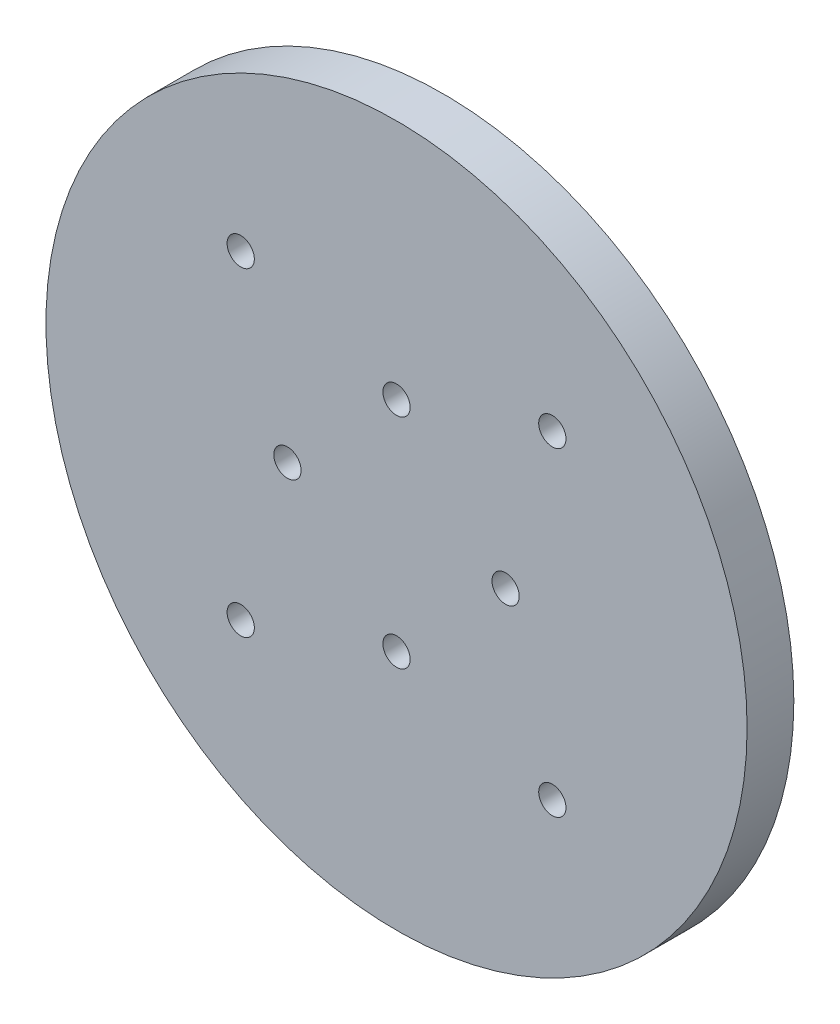
SolidWorks part; units mm, degrees
ref_plane "Front Plane" through (0, 0, 0) normal (0, 0, 1) x (1, 0, 0)
ref_plane "Top Plane" through (0, 0, 0) normal (0, 1, 0) x (1, 0, 0)
ref_plane "Right Plane" through (0, 0, 0) normal (1, 0, 0) x (0, 0, -1)
sketch "Sketch1" plane through (0, 0, 0) normal (0, 0, 1) x (1, 0, 0)
  circle A0 centre (0, 0) radius 45
  dimension "D1" = 90
extrude "Boss-Extrude1" add sketch "Sketch1" along normal blind 6
sketch "Sketch2" plane through (0, 0, 0) normal (0, 0, -1) x (-1, 0, 0)
  circle A0 centre (0, 0) radius 22
  dimension "D1" = 44
extrude "Boss-Extrude2" add sketch "Sketch2" along normal blind 6
sketch "Sketch3" plane through (0, 0, -6) normal (0, 0, -1) x (-1, 0, 0)
  circle A0 centre (0, 0) radius 20.1
  dimension "D1" = 40.2
extrude "Boss-Extrude3" add sketch "Sketch3" along normal blind 4.7
sketch "Sketch4" plane through (0, 0, -10.7) normal (0, 0, -1) x (-1, 0, 0)
  circle A0 centre (0, 0) radius 18.1
  dimension "D1" = 36.2
extrude "Cut-Extrude1" cut sketch "Sketch4" against normal blind 11
sketch "Sketch5" plane through (0, 0, 0.3) normal (0, 0, -1) x (-1, 0, 0)
  circle A4 centre (14, 0) radius 1.75
  circle A5 centre (0, -14) radius 1.75
  circle A6 centre (-14, 0) radius 1.75
  circle A7 centre (0, 14) radius 1.75
  point P11 (0, 0)
  point P12 (0, 0)
  dimension "D1" = 3.5
  dimension "D2" = 14
  dimension "D3" = 4
extrude "Cut-Extrude2" cut sketch "Sketch5" against normal through all
sketch "Sketch6" plane through (0, 0, 0.3) normal (0, 0, -1) x (-1, 0, 0)
  line L0 (20, -20.5) -> (20, 20.5)
  line L1 (0, 0) -> (0, -39.3338)
  circle A0 centre (20, -20.5) radius 1.75
  circle A1 centre (-20, 20.5) radius 1.75
  circle A2 centre (-20, -20.5) radius 1.75
  circle A3 centre (20, 20.5) radius 1.75
  point P3 (20, 0)
  dimension "D3" = 3.5
  dimension "D1" = 41
  dimension "D2" = 20
  dimension "D5" = 41
  dimension "D4" = 2
extrude "Cut-Extrude3" cut sketch "Sketch6" against normal through all both and the other way through all contours A2 | A1 | A3 | A0
sketch "Sketch7" plane through (0, 0, 0) normal (0, 0, 1) x (1, 0, 0)
  circle A0 centre (20, 20.5) radius 2.9
  circle A1 centre (-20, 20.5) radius 2.9
  circle A2 centre (-20, -20.5) radius 2.9
  circle A3 centre (20, -20.5) radius 2.9
  dimension "D1" = 5.8
  dimension "D2" = 5.8
  dimension "D3" = 5.8
  dimension "D4" = 5.8
extrude "Cut-Extrude5" cut sketch "Sketch7" along normal blind 3.3
